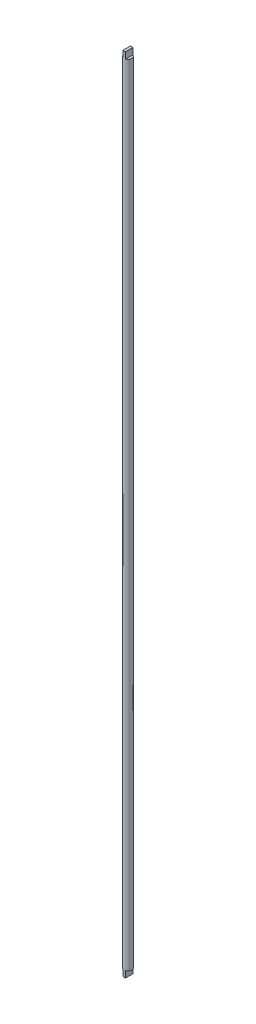
SolidWorks part; units mm, degrees
ref_plane "Front Plane" through (0, 0, 0) normal (0, 0, 1) x (1, 0, 0)
ref_plane "Top Plane" through (0, 0, 0) normal (0, 1, 0) x (1, 0, 0)
ref_plane "Right Plane" through (0, 0, 0) normal (1, 0, 0) x (0, 0, -1)
sketch "Sketch1" plane through (0, 0, 0) normal (0, 1, 0) x (1, 0, 0)
  circle A0 centre (0, 0) radius 3
extrude "Boss-Extrude1" add sketch "Sketch1" along normal blind 616.37
sketch "Sketch2" plane through (0, 616.37, 0) normal (0, 1, 0) x (1, 0, 0)
  line L1 (-1, -3) -> (1, -3)
  line L2 (-1, -3) -> (-1, 3)
  line L3 (-1, 3) -> (1, 3)
  line L4 (1, -3) -> (1, 3)
  line L5 (-1, -3) -> (1, 3) construction
  line L6 (-1, 3) -> (1, -3) construction
  circle A0 centre (0, 0) radius 3
  point P0 (0, 0)
  circle M5 centre (0, 0) radius 3
extrude "Boss-Extrude3" add sketch "Sketch2" along normal blind 5 contours L4 L2 M5
sketch "Sketch4" plane through (0, 621.37, 0) normal (0, 1, 0) x (1, 0, 0)
  line L1 (-1, -2.8284) -> (1, -2.8284)
  line L2 (-1, -2.8284) -> (-1, 2.8284)
  line L3 (-1, 2.8284) -> (1, 2.8284)
  line L4 (1, -2.8284) -> (1, 2.8284)
  line L5 (-1, -2.8284) -> (1, 2.8284) construction
  line L6 (-1, 2.8284) -> (1, -2.8284) construction
  circle A0 centre (0, 0) radius 3
  arc M6 (-1, -2.8284) -> (1, -2.8284) centre (0, 0) ccw
  line M7 (1, -2.8284) -> (1, 2.8284)
  arc M8 (1, 2.8284) -> (-1, 2.8284) centre (0, 0) ccw
  line M9 (-1, 2.8284) -> (-1, -2.8284)
extrude "Boss-Extrude4" add sketch "Sketch4" against normal blind 641.64 contours L3 L1 M9 M7 | L1 M6 | L3 M8
sketch "Sketch5" plane through (0, -20.27, 0) normal (0, -1, 0) x (1, 0, 0)
  line L1 (-1, -2.8284) -> (1, -2.8284)
  line L2 (-1, -2.8284) -> (-1, 2.8284)
  line L3 (-1, 2.8284) -> (1, 2.8284)
  line L4 (1, -2.8284) -> (1, 2.8284)
  line L5 (-1, -2.8284) -> (1, 2.8284) construction
  line L6 (-1, 2.8284) -> (1, -2.8284) construction
  circle A0 centre (0, 0) radius 3
  line M2 (1, -2.8284) -> (1, 2.8284)
  arc M3 (1, 2.8284) -> (-1, 2.8284) centre (0, 0) ccw
  line M4 (-1, 2.8284) -> (-1, -2.8284)
  arc M5 (-1, -2.8284) -> (1, -2.8284) centre (0, 0) ccw
extrude "Cut-Extrude2" cut sketch "Sketch5" against normal blind 15.27 contours L1 M5 | L3 L1 M4 M2 | L3 M3
